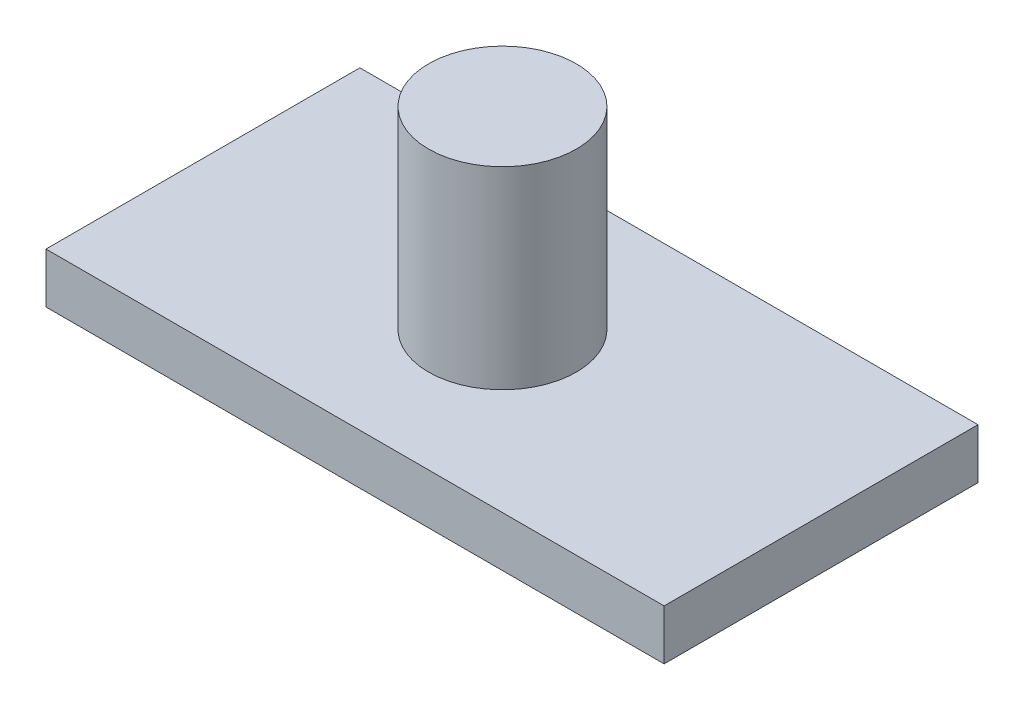
SolidWorks part; units mm, degrees
ref_plane "Front Plane" through (0, 0, 0) normal (0, 0, 1) x (1, 0, 0)
ref_plane "Top Plane" through (0, 0, 0) normal (0, 1, 0) x (1, 0, 0)
ref_plane "Right Plane" through (0, 0, 0) normal (1, 0, 0) x (0, 0, -1)
sketch "Sketch1" plane through (0, 0, 0) normal (0, 1, 0) x (1, 0, 0)
  line L1 (0, 0) -> (81.28, 0)
  line L2 (0, 0) -> (0, -41.275)
  line L3 (0, -41.275) -> (81.28, -41.275)
  line L4 (81.28, 0) -> (81.28, -41.275)
extrude "Boss-Extrude1" add sketch "Sketch1" along normal blind 6.604
sketch "Sketch2" plane through (0, 6.604, 0) normal (0, 1, 0) x (1, 0, 0)
  circle A0 centre (39.1715, -20.4216) radius 9.7164
extrude "Boss-Extrude2" add sketch "Sketch2" along normal blind 25.4
